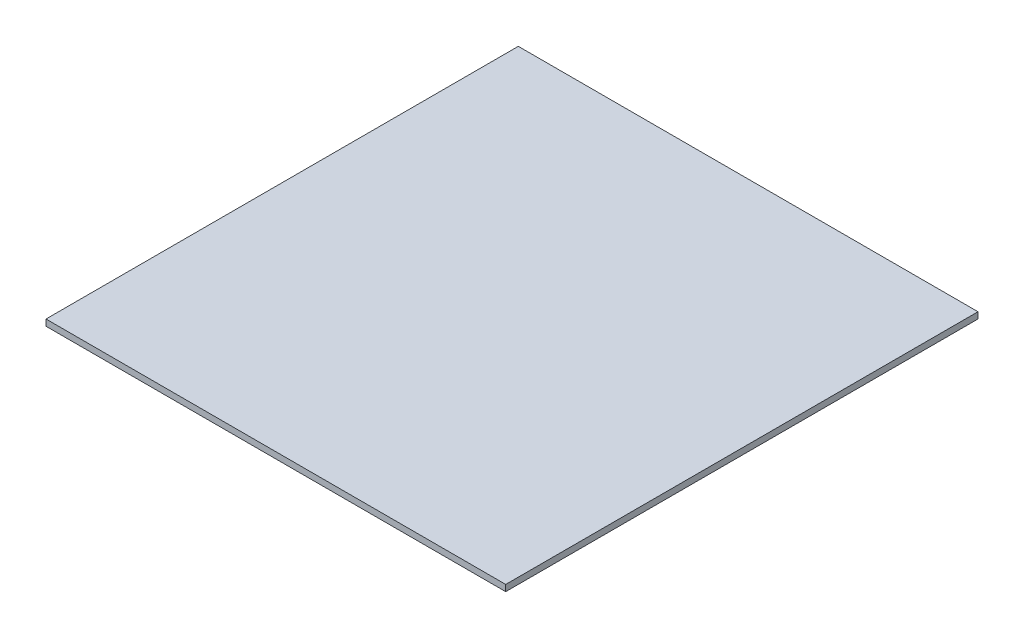
SolidWorks part; units mm, degrees
ref_plane "Front Plane" through (0, 0, 0) normal (0, 0, 1) x (1, 0, 0)
ref_plane "Top Plane" through (0, 0, 0) normal (0, 1, 0) x (1, 0, 0)
ref_plane "Right Plane" through (0, 0, 0) normal (1, 0, 0) x (0, 0, -1)
sketch "Sketch1" plane through (0, 0, 0) normal (0, 0, 1) x (1, 0, 0)
  line L0 (73, -75) -> (73, 75) construction
  line L1 (-73, -75) -> (73, -75)
  line L2 (-73, -75) -> (-73, -73)
  line L3 (-73, -73) -> (73, -73)
  line L4 (73, -75) -> (73, -73)
  dimension "D1" = 2
extrude "Boss-Extrude1" add sketch "Sketch1" along normal up to surface (150 mm away)
